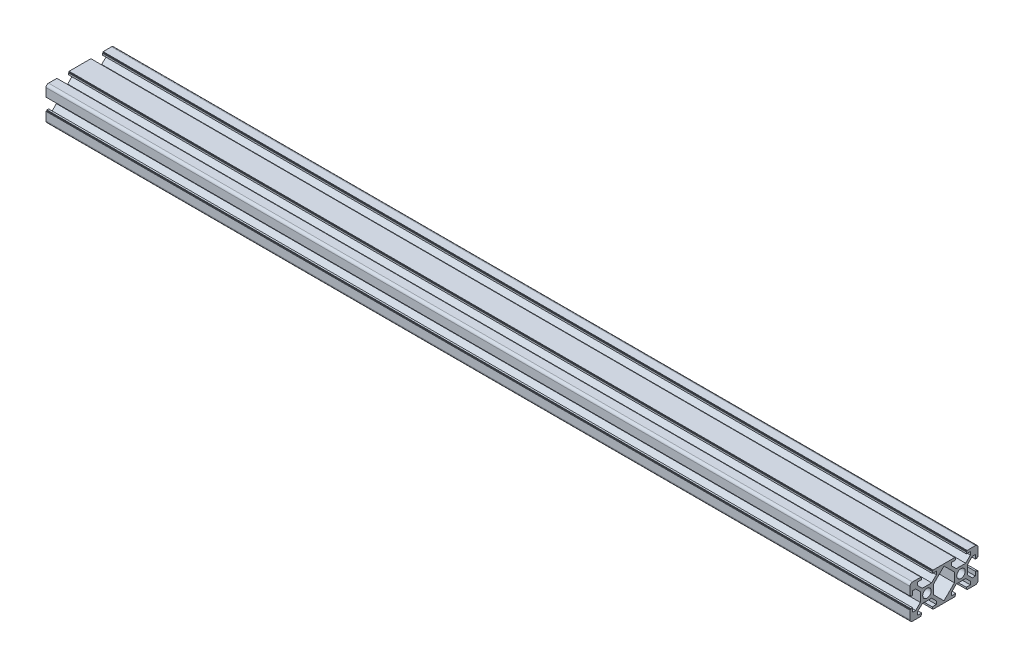
SolidWorks part; units mm, degrees
ref_plane "前视基准面" through (0, 0, 0) normal (0, 0, 1) x (1, 0, 0)
ref_plane "上视基准面" through (0, 0, 0) normal (0, 1, 0) x (1, 0, 0)
ref_plane "右视基准面" through (0, 0, 0) normal (1, 0, 0) x (0, 0, -1)
sketch "草图1" plane through (0, 0, 0) normal (0, 0, 1) x (1, 0, 0)
  line L0 (0, 0) -> (508, 0)
other "铝型材 20 X 40 X T1.5(1)"
ref_plane "基准面5" through (0, 0, 0) normal (1, 0, 0) x (0, 1, 0)
sketch "Sketch11" plane through (0, 0, 0) normal (1, 0, 0) x (0, 1, 0)
  line L0 (-3.6, 10) -> (-3.6, 9.5)
  line L1 (-3.6, 9.5) -> (-3.1, 9.5)
  line L2 (-3.1, 9.5) -> (-3.1, 8.5)
  line L3 (-3.1, 8.5) -> (-5.5, 8.5)
  line L4 (8.85, -10) -> (2.75, -3.9)
  line L5 (-10, -16.4) -> (-10, -3.6)
  line L6 (8.5, 10) -> (3.6, 10)
  line L7 (10, 8.5) -> (10, 3.6)
  line L8 (0, 14.8756) -> (0, 0) construction
  line L9 (0, 0) -> (10, 0) construction
  line L10 (-5.5, 8.5) -> (-5.5, 6.65)
  line L11 (-5.5, 6.65) -> (-2.75, 3.9)
  line L12 (-2.75, 3.9) -> (2.75, 3.9)
  line L13 (5.5, 6.65) -> (2.75, 3.9)
  line L14 (5.5, 8.5) -> (5.5, 6.65)
  line L15 (3.1, 8.5) -> (5.5, 8.5)
  line L16 (3.1, 9.5) -> (3.1, 8.5)
  line L17 (3.6, 9.5) -> (3.1, 9.5)
  line L18 (3.6, 10) -> (3.6, 9.5)
  line L19 (-3.6, 10) -> (-8.5, 10)
  line L20 (10, 3.6) -> (9.5, 3.6)
  line L21 (9.5, 3.6) -> (9.5, 3.1)
  line L22 (9.5, 3.1) -> (8.5, 3.1)
  line L23 (8.5, 3.1) -> (8.5, 5.5)
  line L24 (8.5, 5.5) -> (6.65, 5.5)
  line L25 (6.65, 5.5) -> (3.9, 2.75)
  line L26 (3.9, 2.75) -> (3.9, -2.75)
  line L27 (6.65, -5.5) -> (3.9, -2.75)
  line L28 (8.5, -5.5) -> (6.65, -5.5)
  line L29 (8.5, -3.1) -> (8.5, -5.5)
  line L30 (9.5, -3.1) -> (8.5, -3.1)
  line L31 (9.5, -3.6) -> (9.5, -3.1)
  line L32 (10, -3.6) -> (9.5, -3.6)
  line L33 (8.85, -10) -> (2.75, -16.1)
  line L34 (-8.85, -10) -> (-2.75, -16.1)
  line L35 (-8.85, -10) -> (-2.75, -3.9)
  line L39 (2.75, -3.9) -> (-2.75, -3.9)
  line L46 (-10, -3.6) -> (-9.5, -3.6)
  line L47 (-9.5, -3.6) -> (-9.5, -3.1)
  line L48 (-9.5, -3.1) -> (-8.5, -3.1)
  line L49 (-8.5, -3.1) -> (-8.5, -5.5)
  line L50 (-8.5, -5.5) -> (-6.65, -5.5)
  line L51 (-6.65, -5.5) -> (-3.9, -2.75)
  line L52 (-3.9, -2.75) -> (-3.9, 2.75)
  line L53 (-6.65, 5.5) -> (-3.9, 2.75)
  line L54 (-8.5, 5.5) -> (-6.65, 5.5)
  line L55 (-8.5, 3.1) -> (-8.5, 5.5)
  line L56 (-9.5, 3.1) -> (-8.5, 3.1)
  line L57 (-9.5, 3.6) -> (-9.5, 3.1)
  line L58 (-10, 3.6) -> (-9.5, 3.6)
  line L60 (-10, 3.6) -> (-10, 8.5)
  line L61 (10, -3.6) -> (10, -16.4)
  line L66 (-8.5, -30) -> (-3.6, -30)
  line L67 (-10, -28.5) -> (-10, -23.6)
  line L72 (-2.75, -16.1) -> (2.75, -16.1)
  line L80 (10, -16.4) -> (9.5, -16.4)
  line L81 (9.5, -16.4) -> (9.5, -16.9)
  line L82 (9.5, -16.9) -> (8.5, -16.9)
  line L83 (8.5, -16.9) -> (8.5, -14.5)
  line L84 (8.5, -14.5) -> (6.65, -14.5)
  line L85 (6.65, -14.5) -> (3.9, -17.25)
  line L86 (3.9, -17.25) -> (3.9, -22.75)
  line L87 (6.65, -25.5) -> (3.9, -22.75)
  line L88 (8.5, -25.5) -> (6.65, -25.5)
  line L89 (8.5, -23.1) -> (8.5, -25.5)
  line L90 (9.5, -23.1) -> (8.5, -23.1)
  line L91 (9.5, -23.6) -> (9.5, -23.1)
  line L92 (10, -23.6) -> (9.5, -23.6)
  line L93 (3.6, -30) -> (3.6, -29.5)
  line L94 (3.6, -29.5) -> (3.1, -29.5)
  line L95 (3.1, -29.5) -> (3.1, -28.5)
  line L96 (3.1, -28.5) -> (5.5, -28.5)
  line L97 (5.5, -28.5) -> (5.5, -26.65)
  line L98 (5.5, -26.65) -> (2.75, -23.9)
  line L99 (2.75, -23.9) -> (-2.75, -23.9)
  line L100 (-5.5, -26.65) -> (-2.75, -23.9)
  line L101 (-5.5, -28.5) -> (-5.5, -26.65)
  line L102 (-3.1, -28.5) -> (-5.5, -28.5)
  line L103 (-3.1, -29.5) -> (-3.1, -28.5)
  line L104 (-3.6, -29.5) -> (-3.1, -29.5)
  line L105 (-3.6, -30) -> (-3.6, -29.5)
  line L106 (-10, -23.6) -> (-9.5, -23.6)
  line L107 (-9.5, -23.6) -> (-9.5, -23.1)
  line L108 (-9.5, -23.1) -> (-8.5, -23.1)
  line L109 (-8.5, -23.1) -> (-8.5, -25.5)
  line L110 (-8.5, -25.5) -> (-6.65, -25.5)
  line L111 (-6.65, -25.5) -> (-3.9, -22.75)
  line L112 (-3.9, -22.75) -> (-3.9, -17.25)
  line L113 (-6.65, -14.5) -> (-3.9, -17.25)
  line L114 (-8.5, -14.5) -> (-6.65, -14.5)
  line L115 (-8.5, -16.9) -> (-8.5, -14.5)
  line L116 (-9.5, -16.9) -> (-8.5, -16.9)
  line L117 (-9.5, -16.4) -> (-9.5, -16.9)
  line L118 (-10, -16.4) -> (-9.5, -16.4)
  line L119 (3.6, -30) -> (8.5, -30)
  line L121 (10, -23.6) -> (10, -28.5)
  line L122 (0, -20) -> (10, -20) construction
  line L125 (3.6, -10) -> (3.6, -9.5) [skipped]
  line L127 (3.6, -9.5) -> (3.1, -9.5) [skipped]
  line L129 (3.1, -9.5) -> (3.1, -8.5) [skipped]
  line L131 (3.1, -8.5) -> (5.5, -8.5) [skipped]
  line L133 (-3.1, -8.5) -> (-5.5, -8.5) [skipped]
  line L135 (-3.1, -9.5) -> (-3.1, -8.5) [skipped]
  line L137 (-3.6, -9.5) -> (-3.1, -9.5) [skipped]
  line L139 (-3.6, -10) -> (-3.6, -9.5) [skipped]
  line L141 (-3.6, -10) -> (-3.6, -10.5) [skipped]
  line L142 (-3.6, -10.5) -> (-3.1, -10.5) [skipped]
  line L143 (-3.1, -10.5) -> (-3.1, -11.5) [skipped]
  line L144 (-3.1, -11.5) -> (-5.5, -11.5) [skipped]
  line L145 (8.5, -10) -> (3.6, -10) [skipped]
  line L146 (3.1, -11.5) -> (5.5, -11.5) [skipped]
  line L147 (3.1, -10.5) -> (3.1, -11.5) [skipped]
  line L148 (3.6, -10.5) -> (3.1, -10.5) [skipped]
  line L149 (3.6, -10) -> (3.6, -10.5) [skipped]
  line L150 (-3.6, -10) -> (-8.5, -10) [skipped]
  line L151 (-10, -16.4) -> (-10, -11.5) [skipped]
  line L152 (10, -11.5) -> (10, -16.4) [skipped]
  line L154 (-5.5, -8.5) -> (-5.5, -6.65) [skipped]
  line L156 (5.5, -8.5) -> (5.5, -6.65) [skipped]
  line L157 (5.5, -11.5) -> (5.5, -13.35) [skipped]
  line L158 (-5.5, -11.5) -> (-5.5, -13.35) [skipped]
  line L160 (-12.2446, -13.3946) -> (-10, -11.15) [skipped]
  line L161 (13.644, -5.206) -> (10, -8.85) [skipped]
  line L163 (12.1963, -13.3463) -> (10, -11.15) [skipped]
  line L164 (-11.1344, -7.7156) -> (-10, -8.85) [skipped]
  circle A0 centre (0, 0) radius 2.5
  arc A1 (-10, 8.5) -> (-8.5, 10) centre (-8.5, 8.5) cw
  arc A2 (10, 8.5) -> (8.5, 10) centre (8.5, 8.5) ccw
  arc A3 (10, -28.5) -> (8.5, -30) centre (8.5, -28.5) cw
  arc A4 (-10, -28.5) -> (-8.5, -30) centre (-8.5, -28.5) ccw
  circle A5 centre (0, -20) radius 2.5
  arc A12 (-10, -11.5) -> (-8.5, -10) centre (-8.5, -11.5) cw [skipped]
  arc A13 (10, -11.5) -> (8.5, -10) centre (8.5, -11.5) ccw [skipped]
  point P0 (-10, 0)
  point P1 (10, 0)
  point P2 (0, 10)
  point P4 (0, 0)
  point P5 (0, -10)
  point P6 (-10, -10)
  point P7 (10, 10)
  point P8 (-10, 10)
  point P12 (-10, -10)
  point P13 (10, -10)
  point P15 (0, -10)
  point P16 (10, -10)
  point P36 (-10, 10)
  point P39 (10, 10)
  point P43 (-10, -20)
  point P44 (10, -20)
  point P62 (0, 0)
  point P88 (0, -30)
  point P89 (0, -20)
  point P90 (-10, -30)
  point P91 (10, -30)
  dimension "D1" = 11
  dimension "D2" = 20
  dimension "D3" = 6.2
  dimension "D4" = 7.2
  dimension "D5" = 6.1
  dimension "D6" = 5
  dimension "D7" = 1.5
  dimension "D8" = 45
  dimension "D14" = 20
  dimension "D15" = 1.5
  dimension "D9" = 0.5
  dimension "D10" = 1
  dimension "D11" = 5.5
  dimension "D12" = 10
  dimension "D13" = 40
  dimension "D16" = 45
  dimension "D17" = 45
  dimension "D18" = 45
  dimension "D19" = 6.2
